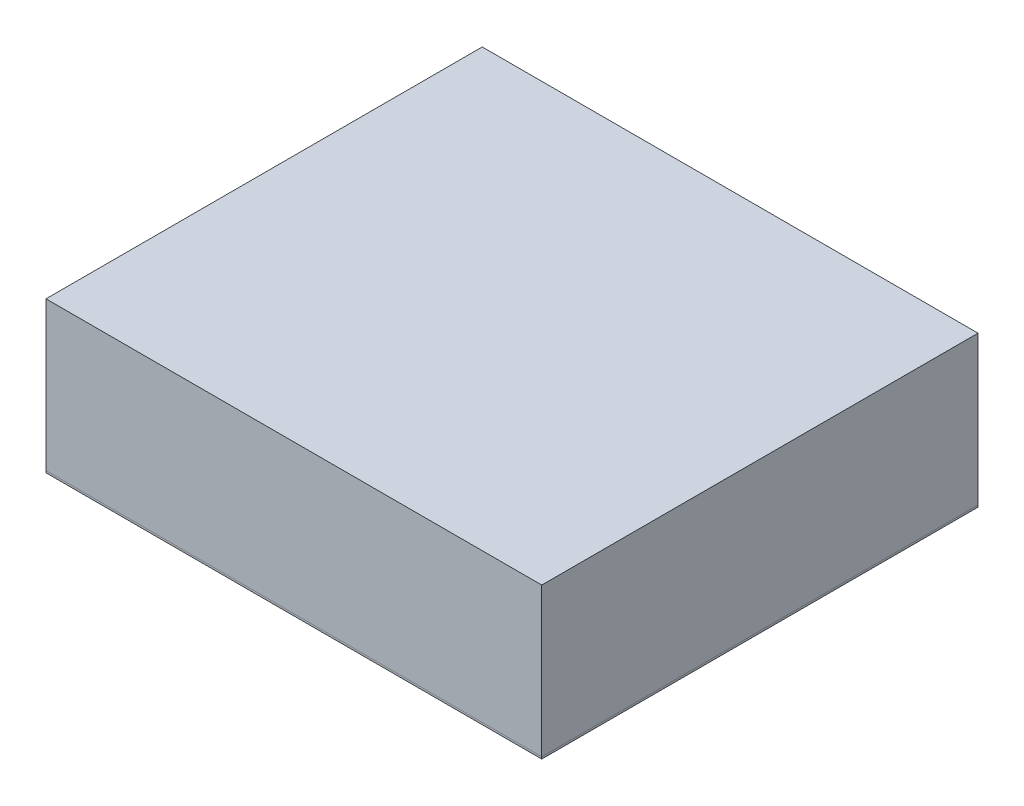
SolidWorks part; units mm, degrees
ref_plane "Front Plane" through (0, 0, 0) normal (0, 0, 1) x (1, 0, 0)
ref_plane "Top Plane" through (0, 0, 0) normal (0, 1, 0) x (1, 0, 0)
ref_plane "Right Plane" through (0, 0, 0) normal (1, 0, 0) x (0, 0, -1)
sketch "Sketch1" plane through (0, 0, 0) normal (0, 0, 1) x (1, 0, 0)
  line L7 (-15.875, -4.7625) -> (15.875, -4.7625)
  line L8 (-15.875, -4.7625) -> (-15.875, 4.7625)
  line L9 (-15.875, 4.7625) -> (15.875, 4.7625)
  line L10 (15.875, -4.7625) -> (15.875, 4.7625)
  line L11 (-15.875, -4.7625) -> (15.875, 4.7625) construction
  line L12 (-15.875, 4.7625) -> (15.875, -4.7625) construction
  point P4 (0, 0)
  point P14 (0, 0)
  dimension "Width" = 31.75
  dimension "Thickness" = 9.525
sketch "Sketch2" plane through (0, 0, 0) normal (0, 1, 0) x (0, 0, -1)
  line L0 (13.97, 15.875) -> (-13.97, 15.875) construction
  point P0 (25.7175, 15.875)
  point P4 (0, 15.875)
  point P6 (-25.7175, 15.875)
  dimension "Length" = 27.94
  dimension "D1" = 39.6875
  dimension "D2" = 39.6875
sketch "Sketch3" plane through (0, 0, 0) normal (0, 0, 1) x (1, 0, 0)
  line L6 (-15.875, 4.7625) -> (15.875, 4.7625)
  line L7 (15.875, 4.7625) -> (15.875, -4.7625)
  line L8 (15.875, -4.7625) -> (-15.875, -4.7625)
  line L9 (-15.875, -4.7625) -> (-15.875, 4.7625)
extrude "Boss-Extrude1" add sketch "Sketch3" along normal mid plane 27.94
sketch "Sketch4" plane through (0, -4.7625, 0) normal (0, -1, 0) x (1, 0, 0)
  line L4 (-15.875, -13.97) -> (15.875, -13.97)
  line L5 (15.875, -13.97) -> (15.875, 13.97)
  line L6 (15.875, 13.97) -> (-15.875, 13.97)
  line L7 (-15.875, 13.97) -> (-15.875, -13.97)
  line L8 (-15.875, -13.97) -> (15.875, -13.97)
  line L9 (15.875, -13.97) -> (15.875, 13.97)
  line L10 (15.875, 13.97) -> (-15.875, 13.97)
  line L11 (-15.875, 13.97) -> (-15.875, -13.97)
  dimension "D1" = 0
extrude "Boss-Extrude2" add sketch "Sketch4" along normal blind 0.127 separate body
equation "\"D1@Boss-Extrude1\" = \"Length@Sketch2\""
equation "\"D1@Sketch2\"=\"Width@Sketch1\" * 1.25"
equation "\"D2@Sketch2\"=\"D1@Sketch2\""
